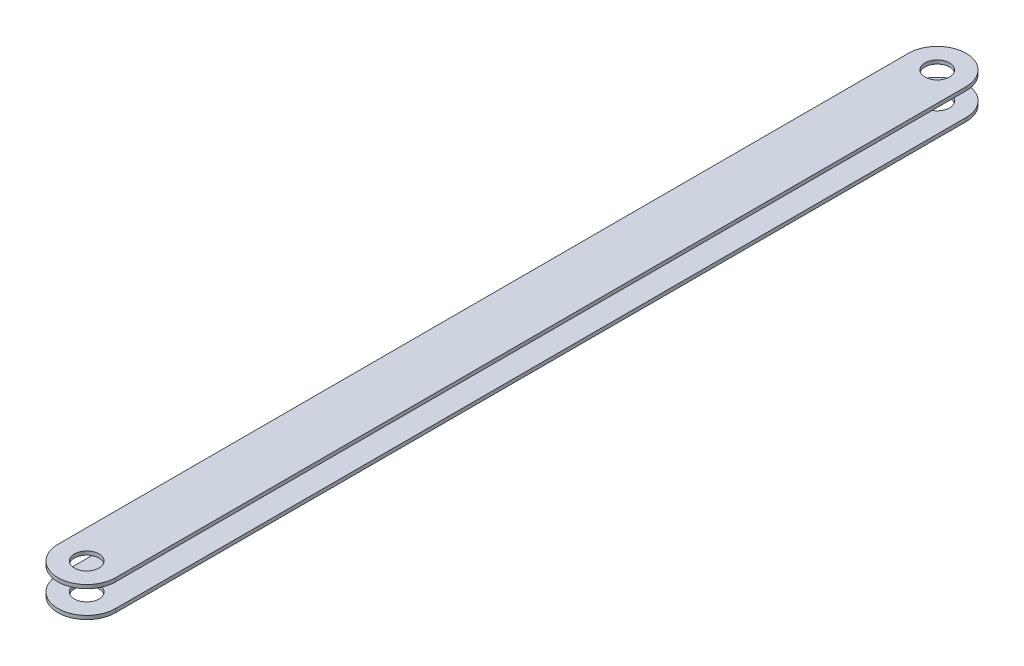
SolidWorks part; units mm, degrees
ref_plane "Front Plane" through (0, 0, 0) normal (0, 0, 1) x (1, 0, 0)
ref_plane "Top Plane" through (0, 0, 0) normal (0, 1, 0) x (1, 0, 0)
ref_plane "Right Plane" through (0, 0, 0) normal (1, 0, 0) x (0, 0, -1)
sketch "Sketch1" plane through (0, 0, 0) normal (0, 0, 1) x (1, 0, 0)
  line L0 (0, 0) -> (0, -4.4)
  line L1 (-0.6, 3.8) -> (0.6, 3.8)
  line L2 (-0.6, 3.8) -> (-0.6, -3.8)
  line L3 (-0.6, -3.8) -> (0.6, -3.8)
  line L4 (0.6, 3.8) -> (0.6, -3.8)
  line L5 (-0.6, 3.8) -> (0.6, -3.8) construction
  line L6 (-0.6, -3.8) -> (0.6, 3.8) construction
  line L7 (-9.5, -3.8) -> (9.5, -3.8)
  line L8 (-9.5, -3.8) -> (-9.5, -5)
  line L9 (-9.5, -5) -> (9.5, -5)
  line L10 (9.5, -3.8) -> (9.5, -5)
  line L11 (-9.5, -3.8) -> (9.5, -5) construction
  line L12 (-9.5, -5) -> (9.5, -3.8) construction
  line L13 (0, 0) -> (6.3315, 0) construction
  line L14 (-9.5, 5) -> (9.5, 3.8) construction
  line L15 (-9.5, 3.8) -> (9.5, 5) construction
  line L16 (9.5, 3.8) -> (9.5, 5)
  line L17 (-9.5, 5) -> (9.5, 5)
  line L18 (-9.5, 3.8) -> (-9.5, 5)
  line L19 (-9.5, 3.8) -> (9.5, 3.8)
  line L20 (-0.6, 3.8) -> (0.6, 3.8)
  point P0 (0, 0)
  point P6 (0, -4.4)
  point P19 (0, 4.4)
  dimension "D1" = 7.6
  dimension "D2" = 1.2
  dimension "D3" = 19
  dimension "D4" = 1.2
extrude "Boss-Extrude1" add sketch "Sketch1" along normal blind 299
sketch "Sketch3" plane through (0, 5, 0) normal (0, 1, 0) x (1, 0, 0)
  line L0 (-9.5, 0) -> (9.5, 0) construction
  line L1 (-14.5, -9.5) -> (-9.5, -9.5)
  line L2 (9.5, -9.5) -> (14.5, -9.5)
  line L3 (9.5, -299) -> (9.5, 0) construction
  line L4 (-9.5, -299) -> (-9.5, 0) construction
  line L12 (9.5, -9.5) -> (4.05, -9.5)
  line L13 (-4.05, -9.5) -> (-9.5, -9.5)
  line L16 (-19.5, -309) -> (19.5, -309)
  line L17 (19.5, -309) -> (19.5, 10)
  line L18 (19.5, 10) -> (-19.5, 10)
  line L19 (-19.5, 10) -> (-19.5, -309)
  line L20 (-19.5, -309) -> (19.5, -309)
  line L21 (19.5, -309) -> (19.5, 10)
  line L22 (19.5, 10) -> (-19.5, 10)
  line L23 (-19.5, 10) -> (-19.5, -309)
  arc A0 (9.5, -9.5) -> (-9.5, -9.5) centre (0, -9.5) ccw
  circle A1 centre (0, -9.5) radius 4.05
  arc A2 (14.5, -9.5) -> (-14.5, -9.5) centre (0, -9.5) ccw
  line M5 (9.5, 0) -> (-9.5, 0)
  line M6 (-9.5, 0) -> (-9.5, -299)
  line M8 (9.5, -299) -> (9.5, 0)
  dimension "D1" = 9.5
  dimension "D2" = 10
  dimension "D4" = 8.1
  dimension "D3" = 5
ref_plane "Plane4" through (0, 0, 149.5) normal (0, 0, 1) x (1, 0, 0)
extrude "Cut-Extrude2" cut sketch "Sketch3" along direction (0, 1, 0) on the side against the normal blind 370 contours A0 M5 M6 | A0 M8 M5 | L2 A2 L1 M6 M5 M8 | A1
mirror "Mirror1" about plane through (0, 0, 149.5) normal (0, 0, 1) of "Cut-Extrude2"
sketch "Sketch6" plane through (-0.6, 0, 0) normal (-1, 0, 0) x (0, 0, 1)
  line L0 (289.5, -3.8) -> (9.5, -3.8) construction
  line L1 (20, -3.8) -> (-1, -3.8)
  line L3 (20, 3.8) -> (-1, 3.8)
  line L4 (-1, -3.8) -> (-1, 3.8)
  line L5 (20, -3.8) -> (-1, 3.8) construction
  line L6 (20, 3.8) -> (-1, -3.8) construction
  line L7 (9.5, 3.8) -> (9.5, -3.8)
  line L9 (285.4947, 3.8) -> (13.5053, 3.8) construction
  line L10 (20, -3.8) -> (20, -3.4641)
  line L11 (20, 3.4641) -> (20, 3.8)
  arc A3 (20.4286, -2.9692) -> (20.4286, 2.9692) centre (20, 0) ccw
  arc A4 (20.4286, 2.9692) -> (20, 3.4641) centre (20.5, 3.4641) cw
  arc A5 (20, -3.4641) -> (20.4286, -2.9692) centre (20.5, -3.4641) cw
  point P0 (9.5, 0)
  point P16 (20, 3)
  point P18 (20, 4.2711)
  dimension "D2" = 0.5
  dimension "D1" = 21
extrude "Cut-Extrude4" cut sketch "Sketch6" along direction (1, 0, 0) on the side against the normal blind 370
mirror "Mirror3" about plane through (0, 0, 149.5) normal (0, 0, 1) of "Cut-Extrude4"
